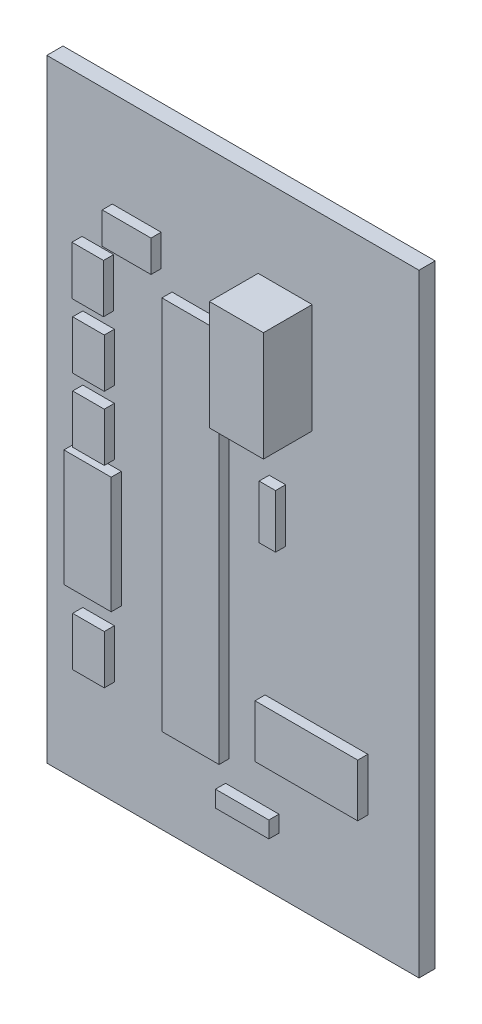
SolidWorks part; units mm, degrees
ref_plane "Front Plane" through (0, 0, 0) normal (0, 0, 1) x (1, 0, 0)
ref_plane "Top Plane" through (0, 0, 0) normal (0, 1, 0) x (1, 0, 0)
ref_plane "Right Plane" through (0, 0, 0) normal (1, 0, 0) x (0, 0, -1)
sketch "Sketch1" plane through (0, 0, 0) normal (0, 0, 1) x (1, 0, 0)
  line L0 (0, 0) -> (36.81, 0)
  line L1 (36.81, 0) -> (36.81, 60.63)
  line L2 (36.81, 60.63) -> (0, 60.63)
  line L3 (0, 60.63) -> (0, 0)
extrude "BOARD" add sketch "Sketch1" along normal blind 1.6 separate body
ref_plane "Plane1" through (0, 0, 1.6) normal (0, 0, 1) x (1, 0, 0)
sketch "Sketch2" plane through (0, 0, 0) normal (0, 0, 1) x (1, 0, 0)
  line L0 (33.16, 22.22) -> (25.26, 22.22)
  line L1 (25.26, 22.22) -> (25.26, 18.42)
  line L2 (25.26, 18.42) -> (33.16, 18.42)
  line L3 (33.16, 18.42) -> (33.16, 22.22)
extrude "TACT_PANA-EVQ-1" add sketch "Sketch2" against normal blind 1 separate body
sketch "Sketch3" plane through (0, 0, 1.6) normal (0, 0, 1) x (1, 0, 0)
  line L0 (6.477, 51.1302) -> (11.303, 51.1302)
  line L1 (11.303, 51.1302) -> (11.303, 48.006)
  line L2 (11.303, 48.006) -> (6.477, 48.006)
  line L3 (6.477, 48.006) -> (6.477, 51.1302)
extrude "C025-030X050-1" add sketch "Sketch3" along normal blind 1 separate body
sketch "Sketch4" plane through (0, 0, 1.6) normal (0, 0, 1) x (1, 0, 0)
  line L0 (3.4798, 42.037) -> (3.4798, 46.863)
  line L1 (3.4798, 46.863) -> (6.604, 46.863)
  line L2 (6.604, 46.863) -> (6.604, 42.037)
  line L3 (6.604, 42.037) -> (3.4798, 42.037)
extrude "C025-030X050-2" add sketch "Sketch4" along normal blind 1 separate body
sketch "Sketch5" plane through (0, 0, 1.6) normal (0, 0, 1) x (1, 0, 0)
  line L0 (6.6802, 40.513) -> (6.6802, 35.687)
  line L1 (6.6802, 35.687) -> (3.556, 35.687)
  line L2 (3.556, 35.687) -> (3.556, 40.513)
  line L3 (3.556, 40.513) -> (6.6802, 40.513)
extrude "C025-030X050-3" add sketch "Sketch5" along normal blind 1 separate body
sketch "Sketch6" plane through (0, 0, 1.6) normal (0, 0, 1) x (1, 0, 0)
  line L0 (6.6802, 34.163) -> (6.6802, 29.337)
  line L1 (6.6802, 29.337) -> (3.556, 29.337)
  line L2 (3.556, 29.337) -> (3.556, 34.163)
  line L3 (3.556, 34.163) -> (6.6802, 34.163)
extrude "C025-030X050-4" add sketch "Sketch6" along normal blind 1 separate body
sketch "Sketch7" plane through (0, 0, 1.6) normal (0, 0, 1) x (1, 0, 0)
  line L0 (6.6802, 15.113) -> (6.6802, 10.287)
  line L1 (6.6802, 10.287) -> (3.556, 10.287)
  line L2 (3.556, 10.287) -> (3.556, 15.113)
  line L3 (3.556, 15.113) -> (6.6802, 15.113)
extrude "C025-030X050-5" add sketch "Sketch7" along normal blind 1 separate body
sketch "Sketch8" plane through (0, 0, 1.6) normal (0, 0, 1) x (1, 0, 0)
  line L0 (31.75, 16.637) -> (31.75, 11.43)
  line L1 (31.75, 11.43) -> (21.59, 11.43)
  line L2 (21.59, 11.43) -> (21.59, 16.637)
  line L3 (21.59, 16.637) -> (31.75, 16.637)
extrude "AB9V-1" add sketch "Sketch8" along normal blind 1 separate body
sketch "Sketch9" plane through (0, 0, 1.6) normal (0, 0, 1) x (1, 0, 0)
  line L0 (12.3825, 46.5455) -> (18.034, 46.5455)
  line L1 (18.034, 46.5455) -> (18.034, 9.398)
  line L2 (18.034, 9.398) -> (12.3825, 9.398)
  line L3 (12.3825, 9.398) -> (12.3825, 46.5455)
extrude "DIL28-1" add sketch "Sketch9" along normal blind 1 separate body
sketch "Sketch10" plane through (0, 0, 0) normal (0, 0, 1) x (1, 0, 0)
  line L0 (31.7735, 35.5835) -> (26.0711, 35.5835)
  line L1 (26.0711, 35.5835) -> (26.0711, 30.1271)
  line L2 (26.0711, 30.1271) -> (31.7735, 30.1271)
  line L3 (31.7735, 30.1271) -> (31.7735, 35.5835)
extrude "RGBLED5050-1" add sketch "Sketch10" against normal blind 1 separate body
sketch "Sketch11" plane through (0, 0, 1.6) normal (0, 0, 1) x (1, 0, 0)
  line L0 (26.245, 52.405) -> (26.245, 41.575)
  line L1 (26.245, 41.575) -> (20.9, 41.575)
  line L2 (20.9, 41.575) -> (20.9, 52.405)
  line L3 (20.9, 52.405) -> (26.245, 52.405)
extrude "TO254P482X997X1968-3P_4.820000-1" add sketch "Sketch11" along normal blind 4.82 separate body
sketch "Sketch12" plane through (0, 0, 1.6) normal (0, 0, 1) x (1, 0, 0)
  line L0 (21.9964, 30.3784) -> (21.9964, 35.6616)
  line L1 (21.9964, 35.6616) -> (23.622, 35.6616)
  line L2 (23.622, 35.6616) -> (23.622, 30.3784)
  line L3 (23.622, 30.3784) -> (21.9964, 30.3784)
extrude "AXIAL-0_3-1" add sketch "Sketch12" along normal blind 1 separate body
sketch "Sketch13" plane through (0, 0, 1.6) normal (0, 0, 1) x (1, 0, 0)
  line L0 (22.9616, 5.4864) -> (17.6784, 5.4864)
  line L1 (17.6784, 5.4864) -> (17.6784, 7.112)
  line L2 (17.6784, 7.112) -> (22.9616, 7.112)
  line L3 (22.9616, 7.112) -> (22.9616, 5.4864)
extrude "AXIAL-0_3-2" add sketch "Sketch13" along normal blind 1 separate body
sketch "Sketch14" plane through (0, 0, 0) normal (0, 0, 1) x (1, 0, 0)
  line L0 (31.3055, 42.3545) -> (31.3055, 54.102)
  line L1 (31.3055, 54.102) -> (27.178, 54.102)
  line L2 (27.178, 54.102) -> (27.178, 42.3545)
  line L3 (27.178, 42.3545) -> (31.3055, 42.3545)
extrude "EG1218-1" add sketch "Sketch14" against normal blind 1 separate body
sketch "Sketch15" plane through (0, 0, 1.6) normal (0, 0, 1) x (1, 0, 0)
  line L0 (7.366, 28.6766) -> (7.366, 17.145)
  line L1 (7.366, 17.145) -> (2.6924, 17.145)
  line L2 (2.6924, 17.145) -> (2.6924, 28.6766)
  line L3 (2.6924, 28.6766) -> (7.366, 28.6766)
extrude "HC49US-1" add sketch "Sketch15" along normal blind 1 separate body
